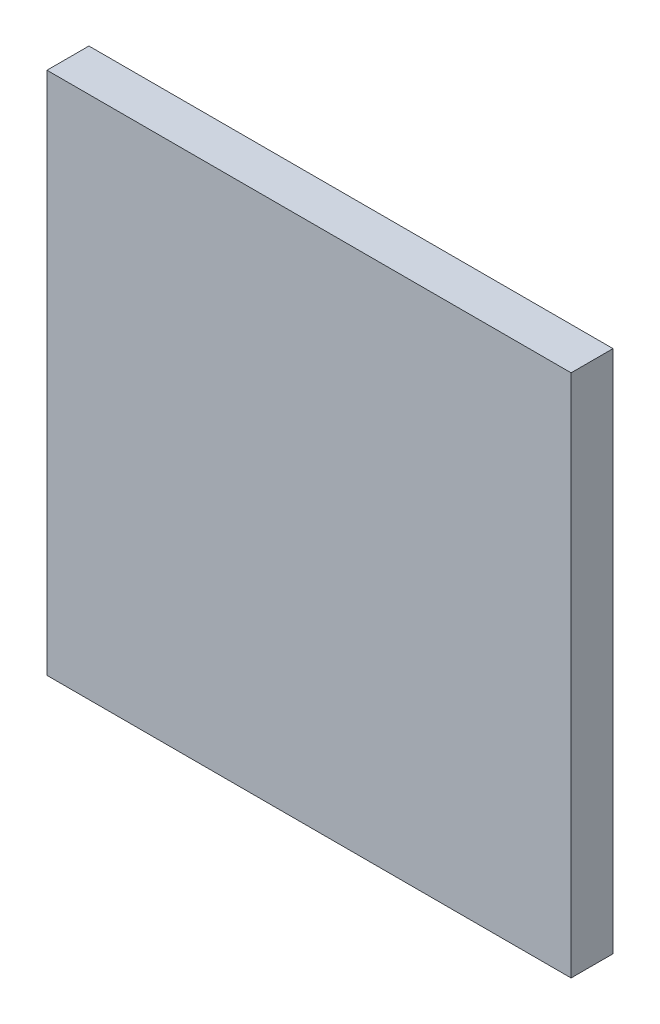
SolidWorks part; units mm, degrees
ref_plane "前视基准面" through (0, 0, 0) normal (0, 0, 1) x (1, 0, 0)
ref_plane "上视基准面" through (0, 0, 0) normal (0, 1, 0) x (1, 0, 0)
ref_plane "右视基准面" through (0, 0, 0) normal (1, 0, 0) x (0, 0, -1)
sketch "草图1" plane through (0, 0, 0) normal (0, 0, 1) x (1, 0, 0)
  line L0 (402.7887, 154.5864) -> (476.6299, 154.5864) construction
  line L1 (441.6175, 187.0122) -> (441.6175, 121.7564) construction
  line L2 (416.6175, 154.3843) -> (416.6175, 179.3843)
  line L3 (416.6175, 179.3843) -> (466.6175, 179.3843)
  line L4 (466.6175, 179.3843) -> (466.6175, 129.3843)
  line L5 (466.6175, 129.3843) -> (416.6175, 129.3843)
  line L6 (416.6175, 129.3843) -> (416.6175, 154.3843)
extrude "凸台-拉伸1" add sketch "草图1" along normal blind 4
